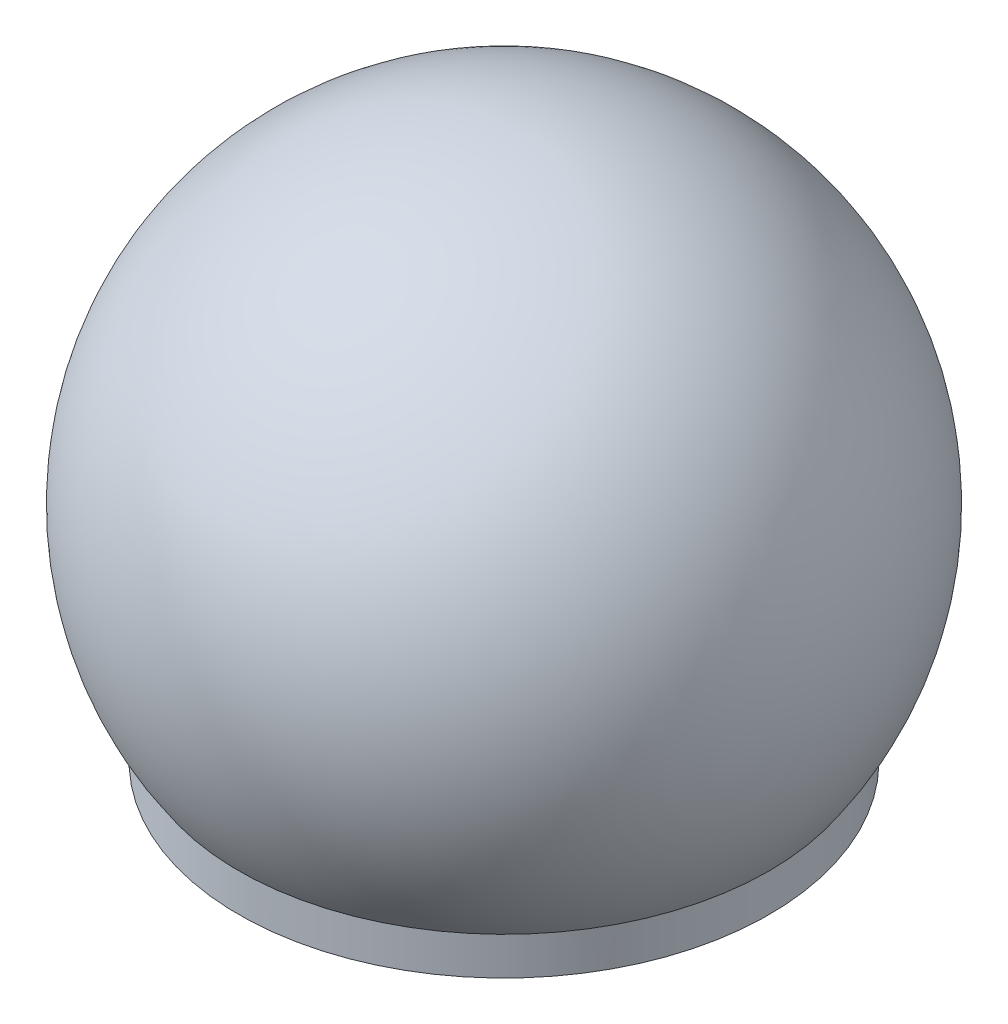
SolidWorks part; units mm, degrees
ref_plane "Front Plane" through (0, 0, 0) normal (0, 0, 1) x (1, 0, 0)
ref_plane "Top Plane" through (0, 0, 0) normal (0, 1, 0) x (1, 0, 0)
ref_plane "Right Plane" through (0, 0, 0) normal (1, 0, 0) x (0, 0, -1)
sketch "Sketch1" plane through (0, 0, 0) normal (0, 0, 1) x (1, 0, 0)
  line L0 (0, 0) -> (0, 65.3751) construction
  line L1 (-1.5875, 0) -> (-22.225, 0)
  line L2 (-22.225, 0) -> (-22.225, 3.175)
  line L3 (-1.5875, 2.1082) -> (-1.5875, 6.35)
  line L4 (-1.5875, 0) -> (-1.5875, 2.1082)
  line L5 (-6.35, 2.1082) -> (-21.1836, 2.1082)
  line L6 (-21.1836, 2.1082) -> (-21.1836, 3.175)
  line L7 (-22.225, 3.175) -> (-26.8406, 9.7667) construction
  line L8 (-6.35, 42.8137) -> (-21.1836, 21.6291)
  line L10 (-1.5875, 6.35) -> (-6.35, 6.35)
  line L11 (-6.35, 6.35) -> (-6.35, 2.1082)
  line L12 (-6.35, 42.8137) -> (0, 42.8137)
  line L13 (0, 42.8137) -> (0, 45.8688)
  line L14 (-21.1836, 3.175) -> (-25.374, 15.6446)
  line L15 (-25.374, 15.6446) -> (-21.1836, 21.6291)
  arc A0 (-22.225, 3.175) -> (0, 45.8688) centre (0, 18.7371) cw
  dimension "D5" = 35
  dimension "D1" = 3.175
  dimension "D2" = 3.175
  dimension "D3" = 1.0414
  dimension "D4" = 2.1082
  dimension "D6" = 44.45
  dimension "D7" = 12.7
  dimension "D8" = 6.35
  dimension "D9" = 35
  dimension "D10" = 12.7
revolve "Revolve1" add sketch "Sketch1" angle 360 about L0
